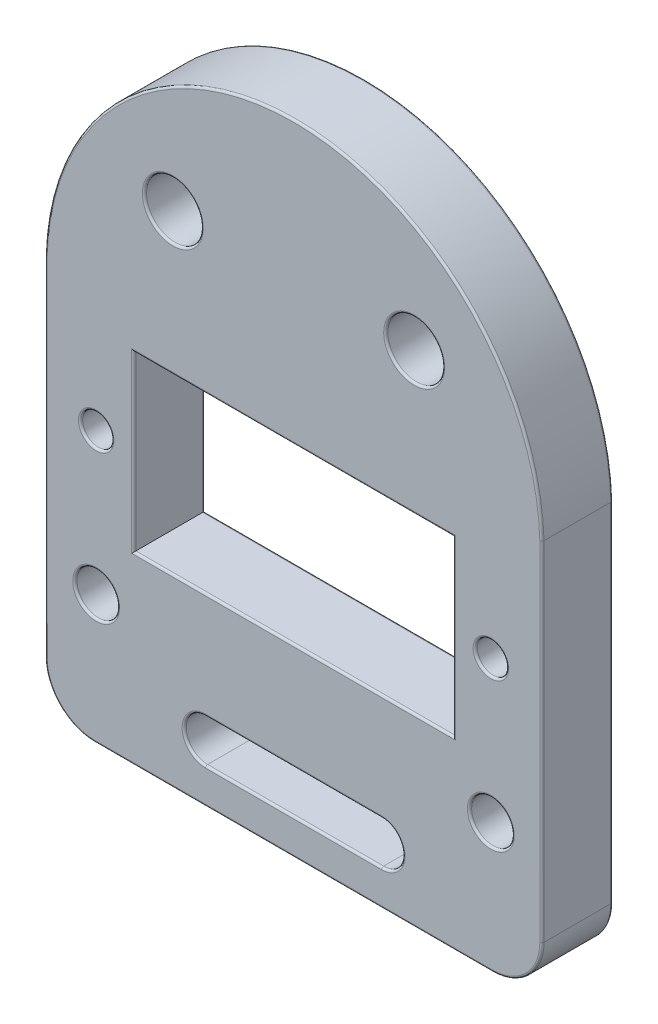
SolidWorks part; units mm, degrees
ref_plane "Płaszczyzna przednia" through (0, 0, 0) normal (0, 0, 1) x (1, 0, 0)
ref_plane "Płaszczyzna górna" through (0, 0, 0) normal (0, 1, 0) x (1, 0, 0)
ref_plane "Płaszczyzna prawa" through (0, 0, 0) normal (1, 0, 0) x (0, 0, -1)
sketch "Szkic1" plane through (0, 0, 0) normal (0, 0, 1) x (1, 0, 0)
  line L0 (0, -19.1) -> (0, 25.9) construction
  line L1 (-11.25, -6.1) -> (11.25, -6.1)
  line L2 (-11.25, -6.1) -> (-11.25, 6.1)
  line L3 (-11.25, 6.1) -> (11.25, 6.1)
  line L4 (11.25, -6.1) -> (11.25, 6.1)
  line L5 (-11.25, -6.1) -> (11.25, 6.1) construction
  line L6 (-11.25, 6.1) -> (11.25, -6.1) construction
  line L7 (-6.2, -15.1) -> (6.2, -15.1) construction
  line L8 (-6.2, -13.6) -> (6.2, -13.6)
  line L9 (-6.2, -16.6) -> (6.2, -16.6)
  line L11 (-17.5, 8.9) -> (17.5, 8.9) construction
  line L12 (-17.5, 8.9) -> (-17.5, -19.1)
  line L13 (-17.5, -19.1) -> (17.5, -19.1)
  line L14 (17.5, 8.9) -> (17.5, -19.1)
  circle A0 centre (-13.9, 0) radius 1.1
  circle A1 centre (-13.9, -10) radius 1.5
  arc A2 (-6.2, -13.6) -> (-6.2, -16.6) centre (-6.2, -15.1) ccw
  arc A3 (6.2, -16.6) -> (6.2, -13.6) centre (6.2, -15.1) ccw
  circle A4 centre (-8.5, 16.1) radius 2
  circle A5 centre (13.9, -10) radius 1.5
  circle A6 centre (13.9, 0) radius 1.1
  circle A7 centre (8.5, 16.1) radius 2
  arc A8 (-17.5, 8.9) -> (17.5, 8.9) centre (0, 8.3926) cw
  point P0 (0, 0)
  point P13 (0, -15.1)
  dimension "D5" = 2.2
  dimension "D7" = 3
  dimension "D11" = 1.5
  dimension "D12" = 4
  dimension "D1" = 22.5
  dimension "D2" = 12.2
  dimension "D3" = 45
  dimension "D4" = 13
  dimension "D6" = 2.65
  dimension "D8" = 10
  dimension "D9" = 12.4
  dimension "D10" = 4
  dimension "D13" = 8.5
  dimension "D14" = 10
  dimension "D15" = 28
  dimension "D16" = 35
extrude "Dodanie-wyciągnięcie1" add sketch "Szkic1" along normal blind 5
fillet "Zaokrąglenie1" radius 3.5 2 edges at (-17.5, -19.1, 2.5) (17.5, -19.1, 2.5)
fillet "Zaokrąglenie2" radius 0.15 40 edges at (6.5, 16.1, 0) (12.4, -10, 0) (7.7, -15.1, 0) (0, -16.6, 0) (-7.7, -15.1, 0) (0, -13.6, 0) (-12.4, -10, 0) (-11.25, 0, 0) (0, 6.1, 0) (11.25, 0, 0) (0, -6.1, 0) (16.4749, -18.0749, 0) (17.5, -3.35, 0) (0, 25.9, 0) (-17.5, -3.35, 0) (-16.4749, -18.0749, 0) (0, -19.1, 0) (-12.8, 0, 0) (-6.5, 16.1, 0) (12.8, 0, 0) (6.5, 16.1, 5) (12.8, 0, 5) (12.4, -10, 5) (-6.5, 16.1, 5) (0, -16.6, 5) (7.7, -15.1, 5) (0, -13.6, 5) (-7.7, -15.1, 5) (0, 25.9, 5) (17.5, -3.35, 5) (16.4749, -18.0749, 5) (0, -19.1, 5) (-16.4749, -18.0749, 5) (-17.5, -3.35, 5) (0, 6.1, 5) (-11.25, 0, 5) (0, -6.1, 5) (11.25, 0, 5) (-12.8, 0, 5) (-12.4, -10, 5)
